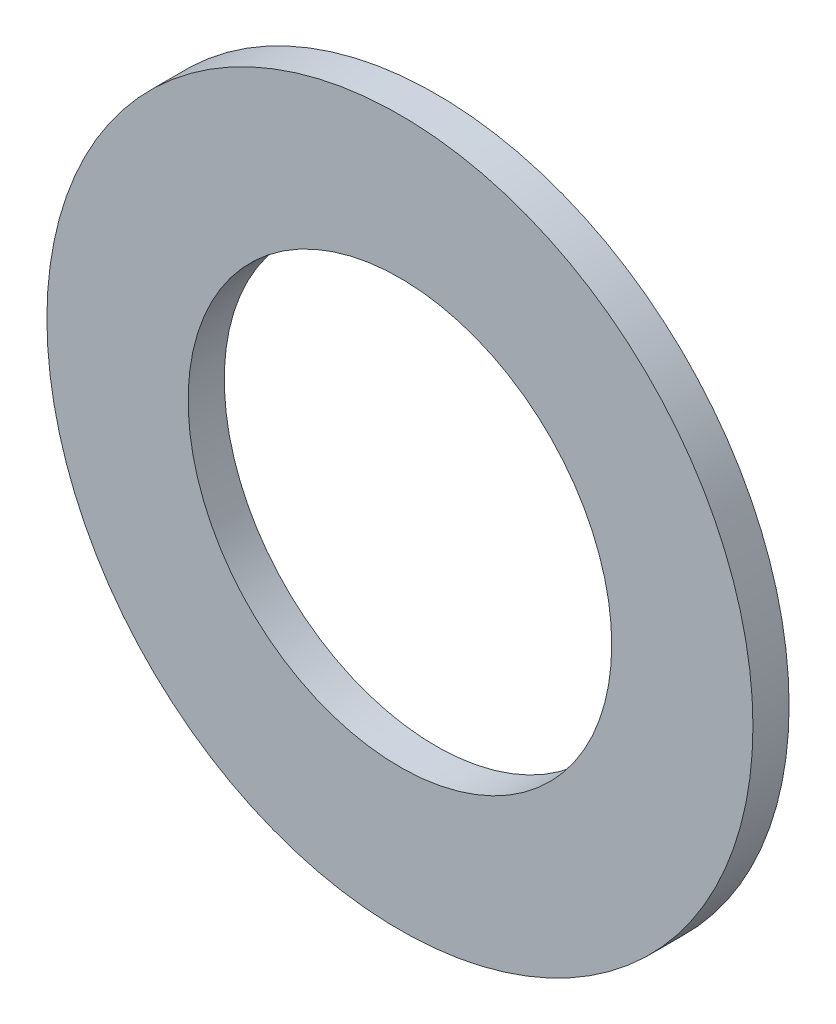
SolidWorks part; units mm, degrees
material "Alloy Steel"
ref_plane "Front Plane" through (0, 0, 0) normal (0, 0, 1) x (1, 0, 0)
ref_plane "Top Plane" through (0, 0, 0) normal (0, 1, 0) x (1, 0, 0)
ref_plane "Right Plane" through (0, 0, 0) normal (1, 0, 0) x (0, 0, -1)
sketch "Sketch1" plane through (0, 0, 0) normal (0, 0, 1) x (1, 0, 0)
  circle A0 centre (0, 0) radius 4.7625
  circle A1 centre (0, 0) radius 7.9375
  dimension "D1" = 9.525
  dimension "D2" = 15.875
extrude "Boss-Extrude1" add sketch "Sketch1" along normal blind 0.8128
